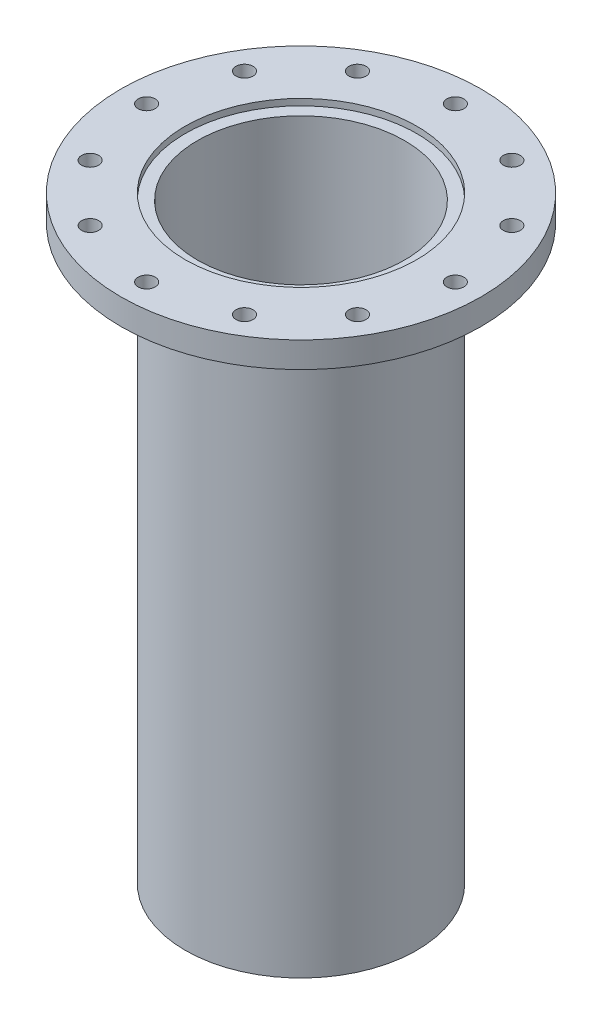
SolidWorks part; units mm, degrees
ref_plane "Front Plane" through (0, 0, 0) normal (0, 0, 1) x (1, 0, 0)
ref_plane "Top Plane" through (0, 0, 0) normal (0, 1, 0) x (1, 0, 0)
ref_plane "Right Plane" through (0, 0, 0) normal (1, 0, 0) x (0, 0, -1)
sketch "Sketch1" plane through (0, 0, 0) normal (0, 0, 1) x (1, 0, 0)
  line L0 (-57.15, 0) -> (-88.9, 0)
  line L1 (-88.9, 0) -> (-88.9, -12.7)
  line L2 (-88.9, -12.7) -> (-57.15, -12.7)
  line L3 (-57.15, -12.7) -> (-57.15, -295.275)
  line L4 (-57.15, -295.275) -> (-51.1302, -295.275)
  line L5 (-51.1302, -295.275) -> (-51.1302, -3.175)
  line L6 (-51.1302, -3.175) -> (-57.15, -3.175)
  line L7 (-57.15, -3.175) -> (-57.15, 0)
  line L8 (0, 0) -> (0, -50.8318) construction
  dimension "D1" = 51.1302
  dimension "D2" = 292.1
  dimension "D3" = 57.15
  dimension "D4" = 12.7
  dimension "D5" = 88.9
  dimension "D6" = 3.175
  dimension "D7" = 57.15
revolve "Revolve1" add sketch "Sketch1" angle 360 about L8
hole_wizard "5/16 Clearance Hole1" positions "Sketch2" profile "Sketch3" hole size "5/16" standard "ANSI Inch" end condition through all
sketch "Sketch2" plane through (0, 0, 0) normal (0, 1, 0) x (1, 0, 0)
  point P0 (-76.2, 0)
  dimension "D1" = 76.2
sketch "Sketch3" plane through (-76.2, 0, 0) normal (1, 0, 0) x (0, 0, 1)
  line L0 (0, 0) -> (0, 295.275)
  line L1 (0, 295.275) -> (4.2164, 295.275)
  line L2 (4.2164, 295.275) -> (4.2164, 0)
  line L5 (4.2164, 0) -> (0, 0)
  line L11 (0, -6.35) -> (0, 107.95) construction
  dimension "Thru Hole Dia." = 8.4328
  dimension "Thru Hole Depth" = 295.275
pattern_circular "CirPattern1" count 12 over 360 about axis through (0, 0, 0) along (0, 1, 0) of "5/16 Clearance Hole1"
